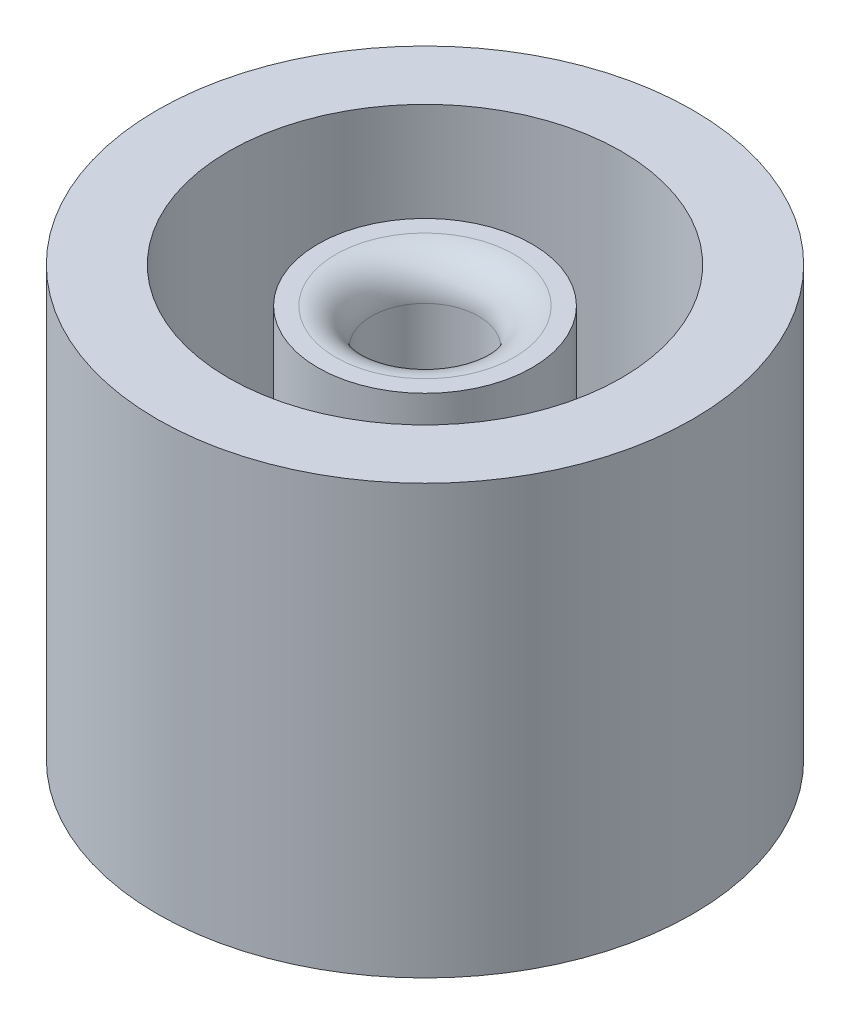
SolidWorks part; units mm, degrees
ref_plane "Front Plane" through (0, 0, 0) normal (0, 0, 1) x (1, 0, 0)
ref_plane "Top Plane" through (0, 0, 0) normal (0, 1, 0) x (1, 0, 0)
ref_plane "Right Plane" through (0, 0, 0) normal (1, 0, 0) x (0, 0, -1)
sketch "Sketch1" plane through (0, 0, 0) normal (0, 1, 0) x (1, 0, 0)
  circle A0 centre (0, 0) radius 13.97
  circle A1 centre (0, 0) radius 19.05
  dimension "D1" = 27.94
  dimension "D2" = 38.1
extrude "Boss-Extrude1" add sketch "Sketch1" along normal blind 30.48
sketch "Sketch2" plane through (0, 0, 0) normal (0, -1, 0) x (1, 0, 0)
  circle A0 centre (0, 0) radius 13.97
extrude "Boss-Extrude2" add sketch "Sketch2" against normal blind 6.35
ref_plane "Plane1" through (0, 0, 16.51) normal (0, 0, 1) x (1, 0, 0)
sketch "Sketch3" plane through (0, 0, 16.51) normal (0, 0, 1) x (1, 0, 0)
  line L0 (-19.05, 0) -> (19.05, 0) construction
  line L1 (0, 101.6) -> (0, 0) construction
  circle A0 centre (0, 101.6) radius 2.2479
  dimension "D1" = 4.4958
  dimension "D2" = 101.6
extrude "Cut-Extrude1" [suppressed] cut sketch "Sketch3" against normal through all and the other way through all contours A0
sketch "Sketch5" plane through (0, 0, 0) normal (1, 0, 0) x (0, 0, -1)
  line L0 (20.955, 0) -> (-20.955, 0) construction
  line L1 (5.08, 12.7) -> (-5.08, 12.7)
  line L2 (5.08, 12.7) -> (5.08, 17.78)
  line L3 (5.08, 17.78) -> (-5.08, 17.78)
  line L4 (-5.08, 12.7) -> (-5.08, 17.78)
  line L5 (19.05, 30.48) -> (-19.05, 30.48) construction
  line L6 (0, 0) -> (0, 12.7) construction
  line L7 (-5.08, 114.3) -> (7.62, 114.3)
  line L8 (-5.08, 88.9) -> (7.62, 88.9)
  line L9 (-5.08, 165.1) -> (5.08, 165.1)
  line L10 (-5.08, 190.5) -> (5.08, 190.5)
  dimension "D1" = 12.7
  dimension "D2" = 12.7
  dimension "D3" = 10.16
  dimension "D4" = 12.7
  dimension "D5" = 12.7
  dimension "D6" = 76.2
  dimension "D7" = 25.4
  dimension "D8" = 25.4
  dimension "D9" = 50.8
extrude "Cut-Extrude5" [suppressed] cut sketch "Sketch5" against normal through all both and the other way through all contours L8 L4 L1 L2 | L9 L4 L7 L2 | L4 L10 L2 L3
sketch "Sketch8" plane through (0, 0, 0) normal (0, 0, 1) x (1, 0, 0)
  line L0 (-19.05, 0) -> (19.05, 0) construction
  line L1 (5.08, 12.7) -> (-5.08, 12.7)
  line L2 (5.08, 12.7) -> (5.08, 17.78)
  line L3 (5.08, 17.78) -> (-5.08, 17.78)
  line L4 (-5.08, 12.7) -> (-5.08, 17.78)
  line L5 (19.05, 30.48) -> (-19.05, 30.48) construction
  line L6 (0, 12.7) -> (0, 0) construction
  line L7 (5.08, 88.9) -> (-5.08, 88.9)
  line L8 (5.08, 114.3) -> (-5.08, 114.3)
  line L9 (5.08, 165.1) -> (-5.08, 165.1)
  line L10 (5.08, 190.5) -> (-5.08, 190.5)
  dimension "D1" = 12.7
  dimension "D2" = 10.16
  dimension "D3" = 12.7
  dimension "D4" = 76.2
  dimension "D5" = 25.4
  dimension "D6" = 25.4
  dimension "D7" = 50.8
extrude "Cut-Extrude6" [suppressed] cut sketch "Sketch8" against normal through all both and the other way through all contours L2 L7 L4 L1 | L2 L9 L4 L8 | L10 L2 L3 L4
sketch "Sketch7" plane through (0, 6.35, 0) normal (0, 1, 0) x (1, 0, 0)
  circle A0 centre (0, 0) radius 5.08
  dimension "D1" = 10.16
extrude "Cut-Extrude4" cut sketch "Sketch7" against normal through all
sketch "Sketch9" plane through (0, 6.35, 0) normal (0, 1, 0) x (1, 0, 0)
  circle A0 centre (0, 0) radius 7.62
  circle A1 centre (0, 0) radius 5.08
  dimension "D1" = 15.24
  dimension "D2" = 2.54
extrude "Boss-Extrude3" add sketch "Sketch9" along normal blind 13.97
sketch "Sketch10" plane through (0, 20.32, 0) normal (0, 1, 0) x (1, 0, 0)
  circle A1 centre (0, 0) radius 7.62 construction
  circle A3 centre (0, 0) radius 7.62
  circle A5 centre (0, 0) radius 3.81
  dimension "D1" = 3.81
extrude "Boss-Extrude4" add sketch "Sketch10" along normal blind 7.62
fillet "Fillet1" radius 2.54 1 edges at (0, 27.94, 3.81)
